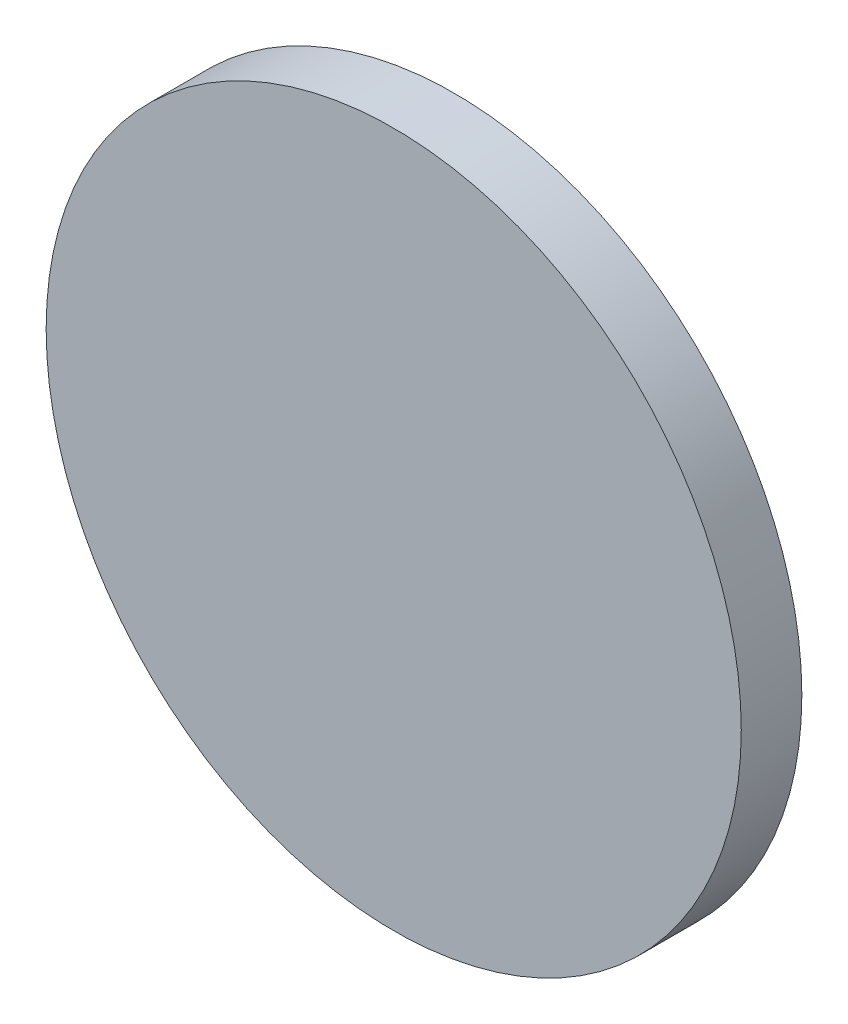
SolidWorks part; units mm, degrees
material "Acrylic (Medium-high impact)"
ref_plane "Front Plane" through (0, 0, 0) normal (0, 0, 1) x (1, 0, 0)
ref_plane "Top Plane" through (0, 0, 0) normal (0, 1, 0) x (1, 0, 0)
ref_plane "Right Plane" through (0, 0, 0) normal (1, 0, 0) x (0, 0, -1)
sketch "Sketch1" plane through (0, 0, 0) normal (0, 0, 1) x (1, 0, 0)
  circle A0 centre (0, 0) radius 57.3785
  dimension "D1" = 114.757
extrude "Boss-Extrude1" add sketch "Sketch1" against normal blind 10
